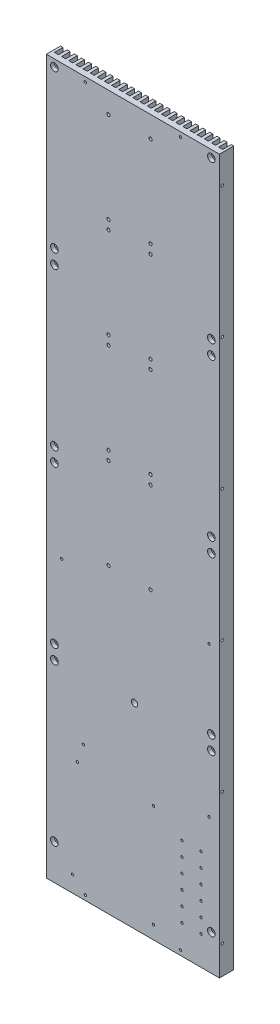
SolidWorks part; units mm, degrees
material "6061 합금"
ref_plane "정면" through (0, 0, 0) normal (0, 0, 1) x (1, 0, 0)
ref_plane "윗면" through (0, 0, 0) normal (0, 1, 0) x (1, 0, 0)
ref_plane "우측면" through (0, 0, 0) normal (1, 0, 0) x (0, 0, -1)
sketch "스케치2" plane through (0, 0, 0) normal (0, 1, 0) x (1, 0, 0)
  line L1 (-91, 15) -> (91, 15)
  line L2 (-91, 15) -> (-91, 0)
  line L3 (-91, 0) -> (91, 0)
  line L4 (91, 15) -> (91, 0)
  dimension "D1" = 182
  dimension "D2" = 15
extrude "보스-돌출1" add sketch "스케치2" along normal blind 750
sketch "스케치3" plane through (0, 0, 0) normal (0, 1, 0) x (1, 0, 0)
  line L0 (-91, 15) -> (91, 15) construction
  line L1 (1.6, 6) -> (5.9, 6)
  line L2 (1.6, 6) -> (1.6, 15)
  line L3 (1.6, 15) -> (5.9, 15)
  line L4 (5.9, 6) -> (5.9, 15)
  line L5 (-91, 0) -> (91, 0) construction
  dimension "D1" = 1.6
  dimension "D2" = 4.3
  dimension "D3" = 6
extrude "컷-돌출1" cut sketch "스케치3" along normal through all
pattern_linear "선형 패턴1" count 12 spacing 7.5 along (1, 0, 0) count 13 spacing 7.5 along (-1, 0, 0) of "컷-돌출1"
hole_wizard "M3 나사 구멍3" positions "스케치7" profile "스케치8" tap size "M3" standard "KS"
sketch "스케치7" plane through (91, 0, 0) normal (1, 0, 0) x (0, 0, -1)
  line L0 (3, 750) -> (3, 720) construction
  line L1 (3, 720) -> (3, 582) construction
  line L2 (3, 582) -> (3, 444) construction
  line L3 (3, 444) -> (3, 306) construction
  line L4 (3, 306) -> (3, 168) construction
  line L5 (3, 168) -> (3, 30) construction
  line L6 (3, 30) -> (3, 0) construction
  line L7 (15, 750) -> (6, 750) construction
  line L8 (15, 0) -> (6, 0) construction
  line L9 (0, 750) -> (0, 0) construction
  point P0 (3, 720)
  point P5 (3, 582)
  point P7 (3, 444)
  point P9 (3, 306)
  point P10 (3, 168)
  point P12 (3, 30)
  dimension "D1" = 3
  dimension "D2" = 30
cosmetic thread "구멍 나사산1" parameters "D1"=8, "D2"=3
cosmetic thread "구멍 나사산2" parameters "D1"=8, "D2"=3
cosmetic thread "구멍 나사산3" parameters "D1"=8, "D2"=3
cosmetic thread "구멍 나사산4" parameters "D1"=8, "D2"=3
cosmetic thread "구멍 나사산5" parameters "D1"=8, "D2"=3
cosmetic thread "구멍 나사산6" parameters "D1"=8, "D2"=3
sketch "스케치8" plane through (91, 720, -3) normal (0, 1, 0) x (0, 0, -1)
  line L0 (0, 0) -> (0, 10.7511)
  line L1 (0, 10.7511) -> (1.25, 10)
  line L2 (1.25, 10) -> (1.25, 0)
  line L5 (1.25, 0) -> (0, 0)
  line L10 (0, 10.7511) -> (-1.25, 10) construction
  line L11 (0, -6.35) -> (0, 107.95) construction
  dimension "탭 드릴 지름" = 2.5
  dimension "탭 드릴 깊이" = 10
  dimension "드릴 각도" = 118
mirror "대칭 복사1" about plane through (0, 0, 0) normal (1, 0, 0) of "M3 나사 구멍3"
cosmetic thread "구멍 나사산15" parameters "D1"=8, "D2"=3
cosmetic thread "구멍 나사산16" parameters "D1"=8, "D2"=3
cosmetic thread "구멍 나사산17" parameters "D1"=8, "D2"=3
cosmetic thread "구멍 나사산18" parameters "D1"=8, "D2"=3
cosmetic thread "구멍 나사산19" parameters "D1"=8, "D2"=3
cosmetic thread "구멍 나사산20" parameters "D1"=8, "D2"=3
hole_wizard "M3 소켓 머리 캡 나사용 카운터보어1" positions "스케치9" profile "스케치10" counterbore size "M3" standard "KS" end condition through all
sketch "스케치9" plane through (0, 0, -15) normal (0, 0, -1) x (-1, 0, 0)
  circle A1 centre (25.6, 412.75) radius 1.3 construction
  point P0 (25.6, 317.25)
  point P3 (-18.6, 317.25)
  point P6 (25.6, 412.75)
  point P10 (-18.6, 412.75)
sketch "스케치10" plane through (-25.6, 317.25, -15) normal (1, 0, 0) x (0, 1, 0)
  line L0 (0, 0) -> (0, 15)
  line L1 (0, 15) -> (1.7, 15)
  line L3 (1.7, 15) -> (1.7, 12)
  line L4 (1.7, 12) -> (3.25, 12)
  line L5 (3.25, 12) -> (3.25, 0)
  line L7 (3.25, 0) -> (0, 0)
  line L11 (0, -6.35) -> (0, 107.95) construction
  dimension "관통 구멍 지름" = 3.4
  dimension "관통 구멍 깊이" = 15
  dimension "카운터보어 지름" = 6.5
  dimension "카운터보어 깊이" = 12
pattern_linear "선형 패턴2" count 4 spacing 105 along (0, 1, 0) of "M3 소켓 머리 캡 나사용 카운터보어1"
hole_wizard "M3 나사 구멍4" positions "스케치11" profile "스케치12" tap size "M3" standard "KS" end condition through all
sketch "스케치11" plane through (0, 0, 0) normal (0, 0, 1) x (1, 0, 0)
  circle A0 centre (-74.84, 298.65) radius 1.98 construction
  circle A1 centre (80.1, 298.65) radius 1.98 construction
  circle A2 centre (80.1, 141.17) radius 1.98 construction
  circle A3 centre (-51.98, 141.17) radius 1.98 construction
  point P0 (-74.84, 298.65)
  point P2 (80.1, 298.65)
  point P4 (80.1, 141.17)
  point P6 (-51.98, 141.17)
  point P7 (-69.5682, 298.1743)
  point P10 (0, 0)
  point P15 (0, 0)
  point P18 (0, 0)
sketch "스케치12" plane through (-74.84, 298.65, 0) normal (1, 0, 0) x (0, -1, 0)
  line L0 (0, 0) -> (0, 15)
  line L1 (0, 15) -> (1.25, 15)
  line L2 (1.25, 15) -> (1.25, 0)
  line L5 (1.25, 0) -> (0, 0)
  line L11 (0, -6.35) -> (0, 107.95) construction
  dimension "관통 탭 드릴 지름" = 2.5
  dimension "관통 탭 드릴 깊이" = 15
cosmetic thread "구멍 나사산7" parameters "D2"=3
cosmetic thread "구멍 나사산8" parameters "D2"=3
cosmetic thread "구멍 나사산9" parameters "D2"=3
cosmetic thread "구멍 나사산10" parameters "D2"=3
hole_wizard "M6 소켓 머리 캡 나사용 카운터보어1" positions "스케치13" profile "스케치14" counterbore size "M6" standard "KS"
sketch "스케치13" plane through (0, 0, -15) normal (0, 0, -1) x (-1, 0, 0)
  point P0 (-1.75, 205.75)
sketch "스케치14" plane through (1.75, 205.75, -15) normal (1, 0, 0) x (0, 1, 0)
  line L0 (0, 0) -> (0, 18.9828)
  line L1 (0, 18.9828) -> (3.3, 17)
  line L2 (3.3, 17) -> (3.3, 10)
  line L3 (3.3, 10) -> (5.5, 10)
  line L4 (5.5, 10) -> (5.5, 0)
  line L5 (5.5, 0) -> (0, 0)
  line L10 (0, 18.9828) -> (-3.3, 17) construction
  line L11 (0, -6.35) -> (0, 107.95) construction
  dimension "구멍 지름" = 6.6
  dimension "구멍 깊이" = 17
  dimension "카운터보어 지름" = 11
  dimension "카운터보어 깊이" = 10
  dimension "드릴 각도" = 118
hole_wizard "M3 나사 구멍5" positions "스케치15" profile "스케치16" tap size "M3" standard "KS"
sketch "스케치15" plane through (0, 0, 0) normal (0, 0, 1) x (1, 0, 0)
  point P0 (-58.35, 122)
  point P3 (21.65, 122)
  point P6 (21.65, 14)
  point P9 (-63.35, 17)
  point P12 (0, 0)
  point P14 (0, 0)
  point P16 (0, 0)
  point P18 (0, 0)
sketch "스케치16" plane through (-58.35, 122, 0) normal (1, 0, 0) x (0, -1, 0)
  line L0 (0, 0) -> (0, 9.2511)
  line L1 (0, 9.2511) -> (1.25, 8.5)
  line L2 (1.25, 8.5) -> (1.25, 0)
  line L5 (1.25, 0) -> (0, 0)
  line L10 (0, 9.2511) -> (-1.25, 8.5) construction
  line L11 (0, -6.35) -> (0, 107.95) construction
  dimension "탭 드릴 지름" = 2.5
  dimension "탭 드릴 깊이" = 8.5
  dimension "드릴 각도" = 118
cosmetic thread "구멍 나사산11" parameters "D1"=6, "D2"=3
cosmetic thread "구멍 나사산12" parameters "D1"=6, "D2"=3
cosmetic thread "구멍 나사산13" parameters "D1"=6, "D2"=3
cosmetic thread "구멍 나사산14" parameters "D1"=6, "D2"=3
hole_wizard "M3 나사 구멍6" positions "스케치17" profile "스케치18" tap size "M3" standard "KS"
sketch "스케치17" plane through (0, 0, 0) normal (0, 0, 1) x (1, 0, 0)
  line L1 (51.65, 90.5) -> (71.65, 90.5) construction
  line L2 (71.65, 90.5) -> (71.65, 75.5) construction
  line L3 (71.65, 75.5) -> (71.65, 60.5) construction
  line L4 (71.65, 60.5) -> (71.65, 45.5) construction
  line L5 (71.65, 45.5) -> (51.65, 45.5) construction
  line L6 (51.65, 45.5) -> (51.65, 60.5) construction
  line L7 (51.65, 60.5) -> (51.65, 75.5) construction
  line L8 (51.65, 75.5) -> (51.65, 90.5) construction
  line L9 (21.65, 122) -> (21.65, 14) construction
  line L11 (51.65, 68) -> (21.65, 68) construction
  line L12 (51.65, 90.5) -> (51.65, 105.5) construction
  line L13 (51.65, 105.5) -> (71.65, 105.5) construction
  line L14 (71.65, 105.5) -> (71.65, 90.5) construction
  line L16 (51.65, 45.5) -> (51.65, 30.5) construction
  line L17 (51.65, 30.5) -> (71.65, 30.5) construction
  line L18 (71.65, 30.5) -> (71.65, 45.5) construction
  point P123 (51.65, 90.5)
  point P124 (71.65, 90.5)
  point P126 (71.65, 75.5)
  point P128 (71.65, 60.5)
  point P130 (71.65, 45.5)
  point P132 (51.65, 45.5)
  point P134 (51.65, 60.5)
  point P136 (51.65, 75.5)
  point P182 (51.65, 105.5)
  point P185 (71.65, 105.5)
  point P188 (71.65, 30.5)
  point P191 (51.65, 30.5)
  dimension "D1" = 15
  dimension "D2" = 20
  dimension "D3" = 30
sketch "스케치18" plane through (51.65, 90.5, 0) normal (1, 0, 0) x (0, -1, 0)
  line L0 (0, 0) -> (0, 11.2511)
  line L1 (0, 11.2511) -> (1.25, 10.5)
  line L2 (1.25, 10.5) -> (1.25, 0)
  line L5 (1.25, 0) -> (0, 0)
  line L10 (0, 11.2511) -> (-1.25, 10.5) construction
  line L11 (0, -6.35) -> (0, 107.95) construction
  dimension "탭 드릴 지름" = 2.5
  dimension "탭 드릴 깊이" = 10.5
  dimension "드릴 각도" = 118
cosmetic thread "구멍 나사산21" parameters "D1"=8, "D2"=3
cosmetic thread "구멍 나사산22" parameters "D1"=8, "D2"=3
cosmetic thread "구멍 나사산23" parameters "D1"=8, "D2"=3
cosmetic thread "구멍 나사산24" parameters "D1"=8, "D2"=3
cosmetic thread "구멍 나사산25" parameters "D1"=8, "D2"=3
cosmetic thread "구멍 나사산26" parameters "D1"=8, "D2"=3
cosmetic thread "구멍 나사산27" parameters "D1"=8, "D2"=3
cosmetic thread "구멍 나사산28" parameters "D1"=8, "D2"=3
cosmetic thread "구멍 나사산36" parameters "D1"=8, "D2"=3
cosmetic thread "구멍 나사산37" parameters "D1"=8, "D2"=3
cosmetic thread "구멍 나사산38" parameters "D1"=8, "D2"=3
cosmetic thread "구멍 나사산39" parameters "D1"=8, "D2"=3
hole_wizard "M3 나사 구멍9" positions "스케치21" profile "스케치22" tap size "M3" standard "KS"
sketch "스케치21" plane through (0, 0, 0) normal (0, 0, 1) x (1, 0, 0)
  line L0 (-91, 750) -> (91, 750) construction
  line L1 (-91, 0) -> (91, 0) construction
  point P0 (-50, 745)
  point P2 (50, 745)
  point P4 (50, 5)
  point P6 (-50, 5)
  dimension "D1" = 50
  dimension "D2" = 50
  dimension "D3" = 5
  dimension "D4" = 5
sketch "스케치22" plane through (-50, 745, 0) normal (1, 0, 0) x (0, -1, 0)
  line L0 (0, 0) -> (0, 11.2511)
  line L1 (0, 11.2511) -> (1.25, 10.5)
  line L2 (1.25, 10.5) -> (1.25, 0)
  line L5 (1.25, 0) -> (0, 0)
  line L10 (0, 11.2511) -> (-1.25, 10.5) construction
  line L11 (0, -6.35) -> (0, 107.95) construction
  dimension "탭 드릴 지름" = 2.5
  dimension "탭 드릴 깊이" = 10.5
  dimension "드릴 각도" = 118
cosmetic thread "구멍 나사산29" parameters "D1"=8, "D2"=3
cosmetic thread "구멍 나사산30" parameters "D1"=8, "D2"=3
cosmetic thread "구멍 나사산31" parameters "D1"=8, "D2"=3
cosmetic thread "구멍 나사산32" parameters "D1"=8, "D2"=3
sketch "스케치23" plane through (0, 0, -15) normal (0, 0, -1) x (-1, 0, 0)
  line L0 (8.25, 0) -> (-8.25, 0) construction
  line L1 (-82.5, 202.5) -> (82.5, 202.5)
  line L2 (-82.5, 202.5) -> (-82.5, 37.5)
  line L3 (-82.5, 37.5) -> (82.5, 37.5)
  line L4 (82.5, 202.5) -> (82.5, 37.5)
  line L5 (-82.5, 202.5) -> (82.5, 37.5) construction
  line L6 (-82.5, 37.5) -> (82.5, 202.5) construction
  line L7 (-90, 210) -> (90, 210)
  line L8 (-90, 210) -> (-90, 30)
  line L9 (-90, 30) -> (90, 30)
  line L10 (90, 210) -> (90, 30)
  line L11 (-90, 210) -> (90, 30) construction
  line L12 (-90, 30) -> (90, 210) construction
  line L13 (0, 8.25) -> (0, -8.25) construction
  point P0 (0, 120)
  point P5 (0, 120)
  dimension "D1" = 180
  dimension "D2" = 165
  dimension "D3" = 120
hole_wizard "M4 소켓 머리 캡 나사용 카운터보어1" positions "스케치24" profile "스케치25" counterbore size "M4" standard "KS" end condition through all
sketch "스케치24" plane through (0, 0, 0) normal (0, 0, 1) x (1, 0, 0)
  point P0 (82.5, 202.5)
  point P3 (82.5, 37.5)
  point P6 (-82.5, 37.5)
  point P9 (-82.5, 202.5)
sketch "스케치25" plane through (82.5, 202.5, 0) normal (1, 0, 0) x (0, -1, 0)
  line L0 (0, 0) -> (0, 15)
  line L1 (0, 15) -> (2.25, 15)
  line L3 (2.25, 15) -> (2.25, 4)
  line L4 (2.25, 4) -> (4, 4)
  line L5 (4, 4) -> (4, 0)
  line L7 (4, 0) -> (0, 0)
  line L11 (0, -6.35) -> (0, 107.95) construction
  dimension "관통 구멍 지름" = 4.5
  dimension "관통 구멍 깊이" = 15
  dimension "카운터보어 지름" = 8
  dimension "카운터보어 깊이" = 4
pattern_linear "선형 패턴3" count 4 spacing 180 along (0, 1, 0) of "M4 소켓 머리 캡 나사용 카운터보어1"
cosmetic thread "구멍 나사산33" parameters "D1"=6, "D2"=3
cosmetic thread "구멍 나사산34" parameters "D1"=6, "D2"=3
cosmetic thread "구멍 나사산35" parameters "D1"=6, "D2"=3
equation "\"Mass\"= \"SW-질량\" / 1000"
